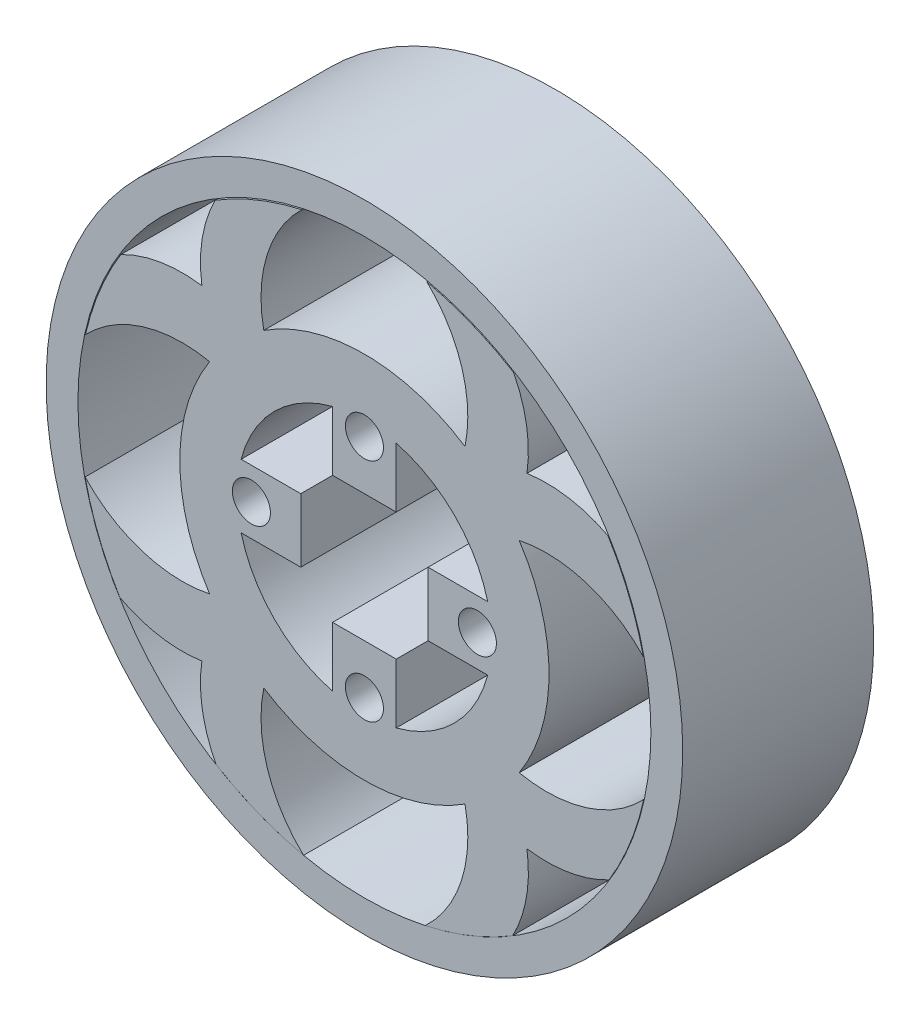
SolidWorks part; units mm, degrees
ref_plane "Front Plane" through (0, 0, 0) normal (0, 0, 1) x (1, 0, 0)
ref_plane "Top Plane" through (0, 0, 0) normal (0, 1, 0) x (1, 0, 0)
ref_plane "Right Plane" through (0, 0, 0) normal (1, 0, 0) x (0, 0, -1)
sketch "Sketch6" plane through (0, 0, 0) normal (0, 0, 1) x (1, 0, 0)
  circle A0 centre (0, 0) radius 20
  circle A1 centre (0, 0) radius 29
  dimension "D1" = 40
  dimension "D2" = 58
extrude "Inner Ring" add sketch "Sketch6" against normal blind 30 separate body
sketch "Sketch7" plane through (0, 0, 0) normal (0, 0, 1) x (1, 0, 0)
  line L2 (-10, 5) -> (-10, -5)
  line L3 (-5, 10) -> (5, 10)
  line L4 (10, 5) -> (10, -5)
  line L5 (-5, -10) -> (5, -10)
  line L14 (-19.3649, 5) -> (-10, 5)
  line L15 (-19.3649, -5) -> (-10, -5)
  line L16 (-5, 19.3649) -> (-5, 10)
  line L17 (5, 19.3649) -> (5, 10)
  line L18 (19.3649, 5) -> (10, 5)
  line L19 (19.3649, -5) -> (10, -5)
  line L20 (5, -19.3649) -> (5, -10)
  line L21 (-5, -19.3649) -> (-5, -10)
  circle A1 centre (0, 0) radius 20
  circle M19 centre (0, 0) radius 20
  dimension "D1" = 20
  dimension "D2" = 20
  dimension "D3" = 10
  dimension "D5" = 10
  dimension "D7" = 10
  dimension "D8" = 10
extrude "Motor Connector Cut" add sketch "Sketch7" against normal blind 30 contours L19 L18 L4 M19 | L17 L16 L3 M19 | L15 L2 L14 M19 | L21 L20 L5 M19
sketch "Sketch8" plane through (0, 0, 0) normal (0, 0, 1) x (1, 0, 0)
  circle A1 centre (0, 17.75) radius 2.987
  circle A2 centre (17.75, 0) radius 2.987
  circle A3 centre (0, -17.75) radius 2.987
  circle A4 centre (-17.75, 0) radius 2.987
  dimension "D1" = 5.974
  dimension "D2" = 5.974
  dimension "D3" = 5.974
  dimension "0.0049m" = 5.974
sketch "Sketch9" plane through (0, 0, 0) normal (0, 0, 1) x (1, 0, 0)
  circle A0 centre (0, 0) radius 50
  circle A18 centre (0, 0) radius 29
  dimension "D2" = 100
extrude "Outside Ring Extrusion" add sketch "Sketch9" against normal blind 30
sketch "Sketch12" plane through (0, 0, 0) normal (0, 0, 1) x (1, 0, 0)
  circle A0 centre (0, 0) radius 27.5
  circle A1 centre (0, 0) radius 45
  dimension "D1" = 55
  dimension "D2" = 90
extrude "Cut-Extrude6" cut sketch "Sketch12" against normal blind 56 and the other way blind 38
extrude "Motor Connector Holes" cut sketch "Sketch8" against normal blind 41 and the other way blind 27
sketch "Sketch10" plane through (0, 0, 0) normal (0, 0, 1) x (1, 0, 0)
  circle A0 centre (0, 0) radius 29
  arc A4 (-24.0947, 20.4191) -> (-41.6064, 16.7952) centre (-29, 0) ccw
  circle A5 centre (0, 0) radius 50
  arc A6 (-0.0957, 0) -> (0, 0.0957) centre (-17.7016, 17.7016) ccw
  arc A9 (-28.6072, 4.7568) -> (-42.4805, -14.6492) centre (-17.7016, -17.7016) ccw
  arc A10 (-20.4191, 24.0947) -> (-38.2638, 23.4049) centre (-28.6072, 4.7568) ccw
  arc A11 (-24.3176, 15.8004) -> (-43.8179, 9.722) centre (-28.6072, -4.7568) ccw
  circle A18 centre (0, 0) radius 29
  arc A19 (14.3758, 42.4453) -> (-4.7568, 28.6072) centre (17.7016, 17.7016) ccw
  circle A20 centre (0, -0.0957) radius 44.9043
  arc A21 (24.3176, -15.8004) -> (43.8731, -9.6638) centre (28.6072, 4.7568) ccw
  arc A22 (43.8179, 9.722) -> (24.3176, 15.8004) centre (28.6072, -4.7568) ccw
  arc A23 (41.6064, 16.7952) -> (21.3966, 19.5752) centre (29, 0) ccw
  arc A24 (49.5968, 4.0954) -> (49.3228, 8.2014) centre (28.6072, 4.7568) ccw
  arc A25 (49.5968, -4.0954) -> (49.5968, 4.0954) centre (29, 0) ccw
  arc A26 (28.6072, -4.7568) -> (42.4628, 14.5092) centre (17.7016, 17.7016) ccw
  arc A27 (42.4805, -14.6492) -> (28.6072, 4.7568) centre (17.7016, -17.7016) ccw
  arc A28 (49.3228, -8.2014) -> (49.5968, -4.0954) centre (28.6072, -4.7568) ccw
  arc A29 (25.5301, 25.5301) -> (23.4328, 38.2096) centre (4.7568, 28.6072) ccw
  arc A30 (23.2856, -38.4907) -> (22.8197, -17.8959) centre (4.7568, -28.6072) ccw
  arc A31 (20.4191, 24.0947) -> (16.8561, 41.5248) centre (0, 29) ccw
  arc A32 (24.0947, -20.4191) -> (41.717, -16.7116) centre (29, 0) ccw
  arc A33 (15.8004, 24.3176) -> (9.8231, 43.721) centre (-4.7568, 28.6072) ccw
  arc A34 (4.7568, 28.6072) -> (-14.3758, 42.4453) centre (-17.7016, 17.7016) ccw
  arc A35 (16.6483, -41.7998) -> (20.4191, -24.0947) centre (0, -29) ccw
  arc A36 (9.5599, -43.9706) -> (15.8004, -24.3176) centre (-4.7568, -28.6072) ccw
  arc A38 (17.8959, -22.8197) -> (38.435, -23.3152) centre (28.6072, -4.7568) ccw
  arc A39 (-14.7836, -42.4967) -> (4.7568, -28.6072) centre (-17.7016, -17.7016) ccw
  arc A40 (-38.435, -23.3152) -> (-20.4191, -24.0947) centre (-28.6072, -4.7568) ccw
  arc A41 (-43.8731, -9.6638) -> (-24.3176, -15.8004) centre (-28.6072, 4.7568) ccw
  arc A43 (-41.717, -16.7116) -> (-21.3966, -19.5752) centre (-29, 0) ccw
  arc A44 (0, -0.0957) -> (-0.0957, 0) centre (-17.7016, -17.7016) ccw
  arc A45 (-42.4628, 14.5092) -> (-28.6072, -4.7568) centre (-17.7016, 17.7016) ccw
  arc A46 (-4.7568, -28.6072) -> (14.7836, -42.4967) centre (17.7016, -17.7016) ccw
  arc A47 (-23.4328, 38.2096) -> (-24.0947, 20.4191) centre (-4.7568, 28.6072) ccw
  arc A48 (-15.8004, -24.3176) -> (-9.5599, -43.9706) centre (4.7568, -28.6072) ccw
  arc A49 (-16.8561, 41.5248) -> (-19.5752, 21.3966) centre (0, 29) ccw
  arc A50 (-20.4191, -24.0947) -> (-16.6483, -41.7998) centre (0, -29) ccw
  arc A51 (-9.8231, 43.721) -> (-15.8004, 24.3176) centre (4.7568, 28.6072) ccw
  arc A52 (-25.5301, -25.5301) -> (-23.2856, -38.4907) centre (-4.7568, -28.6072) ccw
  arc A53 (4.0954, 49.5968) -> (-4.0954, 49.5968) centre (0, 29) ccw
  arc A54 (8.2014, 49.3228) -> (0, 49.0614) centre (4.7568, 28.6072) ccw
  arc A55 (0, 49.0614) -> (-8.2014, 49.3228) centre (-4.7568, 28.6072) ccw
  arc A56 (38.2638, 23.4049) -> (25.5301, 25.5301) centre (28.6072, 4.7568) ccw
  circle A57 centre (-0.0957, 0) radius 27.4043
extrude "Pattern" add sketch "Sketch10" against normal blind 30
